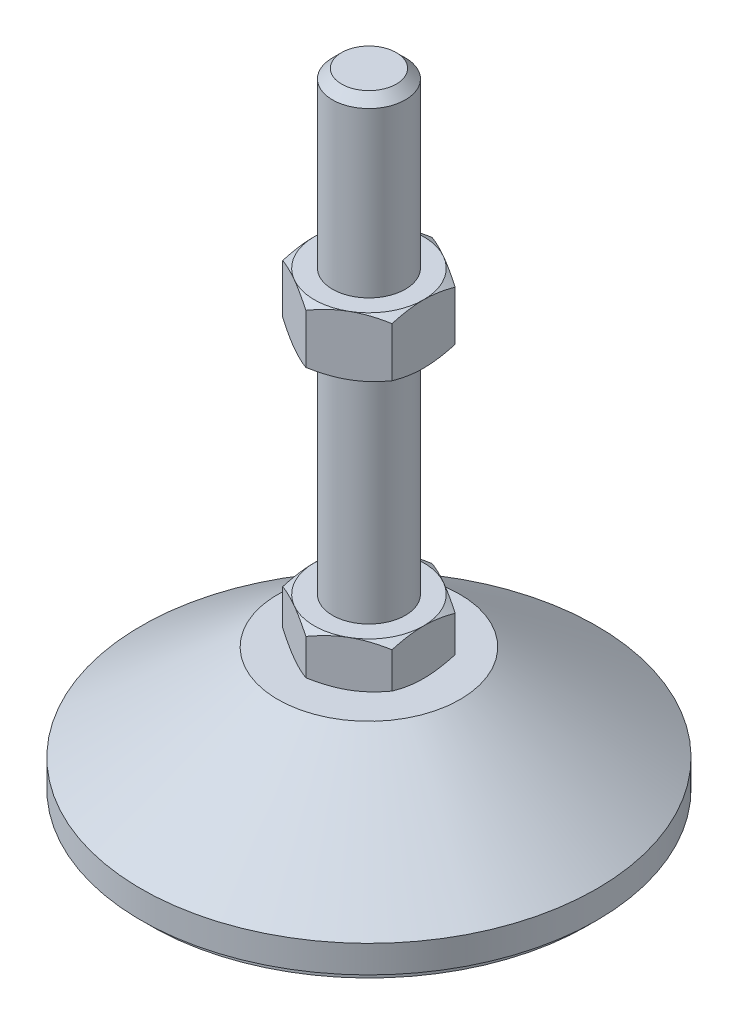
SolidWorks part; units mm, degrees
ref_plane "Спереди" through (0, 0, 0) normal (0, 0, 1) x (1, 0, 0)
ref_plane "Сверху" through (0, 0, 0) normal (0, 1, 0) x (1, 0, 0)
ref_plane "Справа" through (0, 0, 0) normal (1, 0, 0) x (0, 0, -1)
sketch "Эскиз1" plane through (0, 0, 0) normal (0, 0, 1) x (1, 0, 0)
  line L0 (0, 0) -> (-48, 0)
  line L1 (-48, 0) -> (-48, 2)
  line L2 (-48, 2) -> (-50, 2)
  line L3 (-50, 2) -> (-50, 8)
  line L4 (-50, 8) -> (-20, 29)
  line L5 (-20, 29) -> (-8, 29)
  line L12 (-8, 39) -> (-8, 137)
  line L13 (-8, 137) -> (-6, 139)
  line L14 (-6, 139) -> (0, 139)
  line L15 (0, 139) -> (0, 0) construction
  line L16 (-8, 29) -> (0, 29) construction
  line L17 (0, 0) -> (0, 139)
  line L18 (0, 0) -> (0, -7.9595) construction
  line L19 (-8, 39) -> (-8, 29)
  point P8 (-8, 88)
  point P23 (-14, 29)
  dimension "D1" = 16
  dimension "D2" = 29
  dimension "D3" = 10
  dimension "D4" = 100
  dimension "D5" = 8
  dimension "D6" = 2
  dimension "D7" = 45
  dimension "D8" = 40
  dimension "D9" = 2
  dimension "D10" = 100
  dimension "D11" = 6
revolve "Повернуть1" add sketch "Эскиз1" angle 360 about L17
sketch "Эскиз2" plane through (0, 29, 0) normal (0, 1, 0) x (1, 0, 0)
  line L1 (0, 13.8564) -> (-12, 6.9282)
  line L2 (-12, 6.9282) -> (-12, -6.9282)
  line L3 (-12, -6.9282) -> (0, -13.8564)
  line L4 (0, -13.8564) -> (12, -6.9282)
  line L5 (12, -6.9282) -> (12, 6.9282)
  line L6 (12, 6.9282) -> (0, 13.8564)
  circle A0 centre (0, 0) radius 12 construction
  dimension "D1" = 24
extrude "Бобышка-Вытянуть1" add sketch "Эскиз2" along normal up to vertex (10 mm away) up to point (-8, 39, 0)
ref_plane "Плоскость1" through (0, 88, 0) normal (0, 1, 0) x (1, 0, 0)
sketch "Эскиз3" plane through (0, 88, 0) normal (0, 1, 0) x (1, 0, 0)
  line L6 (12, 6.9282) -> (0, 13.8564)
  line L7 (0, 13.8564) -> (-12, 6.9282)
  line L8 (-12, 6.9282) -> (-12, -6.9282)
  line L9 (-12, -6.9282) -> (0, -13.8564)
  line L10 (0, -13.8564) -> (12, -6.9282)
  line L11 (12, -6.9282) -> (12, 6.9282)
  line L12 (12, 6.9282) -> (0, 13.8564)
  line L13 (0, 13.8564) -> (-12, 6.9282)
  line L14 (-12, 6.9282) -> (-12, -6.9282)
  line L15 (-12, -6.9282) -> (0, -13.8564)
  line L16 (0, -13.8564) -> (12, -6.9282)
  line L17 (12, -6.9282) -> (12, 6.9282)
  dimension "D1" = 0
extrude "Бобышка-Вытянуть2" add sketch "Эскиз3" along normal blind 13
sketch "Эскиз4" plane through (0, 0, 0) normal (0, 0, 1) x (1, 0, 0)
  line L0 (-12, 101) -> (-23.2583, 94.5)
  line L1 (-23.2583, 94.5) -> (-23.2583, 101)
  line L2 (-23.2583, 101) -> (-12, 101)
  line L3 (-23.2583, 94.5) -> (-12, 88)
  line L4 (50, 88) -> (-50, 88) construction
  line L5 (-12, 88) -> (-23.2583, 88)
  line L6 (-23.2583, 88) -> (-23.2583, 94.5)
  line L7 (-12, 101) -> (-12, 88) construction
  line L8 (-12, 39) -> (-20.6603, 39)
  line L9 (-20.6603, 39) -> (-20.6603, 34)
  line L10 (-20.6603, 34) -> (-12, 39)
  line L11 (-12, 29) -> (-20.6603, 34)
  line L12 (-20.6603, 34) -> (-20.6603, 29)
  line L13 (-20.6603, 29) -> (-12, 29)
  line L14 (0, 139) -> (0, 96.3793) construction
  dimension "D1" = 30
  dimension "D2" = 30
revolve "Вырез-Повернуть2" cut sketch "Эскиз4" angle 360 about L14
